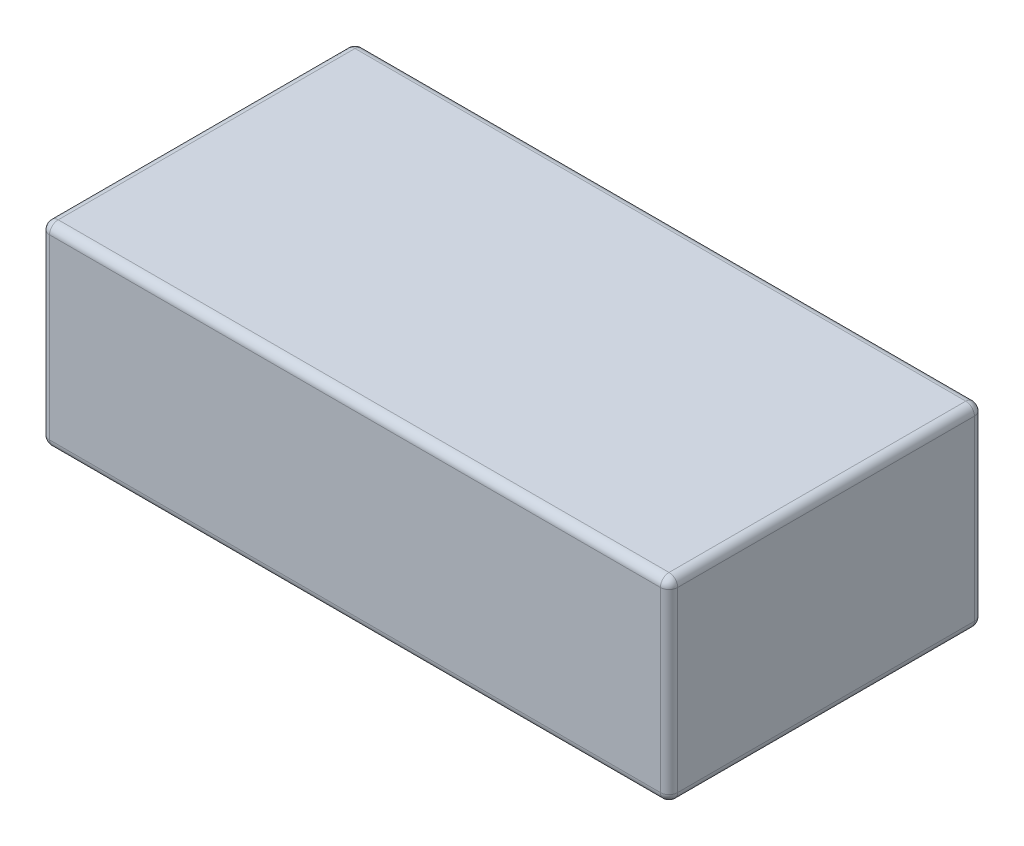
SolidWorks part; units mm, degrees
ref_plane "Front Plane" through (0, 0, 0) normal (0, 0, 1) x (1, 0, 0)
ref_plane "Top Plane" through (0, 0, 0) normal (0, 1, 0) x (1, 0, 0)
ref_plane "Right Plane" through (0, 0, 0) normal (1, 0, 0) x (0, 0, -1)
sketch "Sketch1" plane through (0, 0, 0) normal (0, 1, 0) x (1, 0, 0)
  line L1 (-92.075, 46.0375) -> (92.075, 46.0375)
  line L2 (-92.075, 46.0375) -> (-92.075, -46.0375)
  line L3 (-92.075, -46.0375) -> (92.075, -46.0375)
  line L4 (92.075, 46.0375) -> (92.075, -46.0375)
  line L5 (-92.075, 46.0375) -> (92.075, -46.0375) construction
  line L6 (-92.075, -46.0375) -> (92.075, 46.0375) construction
  point P0 (0, 0)
  dimension "D1" = 92.075
  dimension "D2" = 184.15
extrude "Boss-Extrude1" add sketch "Sketch1" along normal blind 57.15
fillet "Fillet1" radius 2.54 12 edges at (92.075, 28.575, -46.0375) (-92.075, 28.575, -46.0375) (-92.075, 28.575, 46.0375) (92.075, 28.575, 46.0375) (0, 0, -46.0375) (-92.075, 0, 0) (0, 0, 46.0375) (92.075, 0, 0) (0, 57.15, 46.0375) (-92.075, 57.15, 0) (0, 57.15, -46.0375) (92.075, 57.15, 0)
